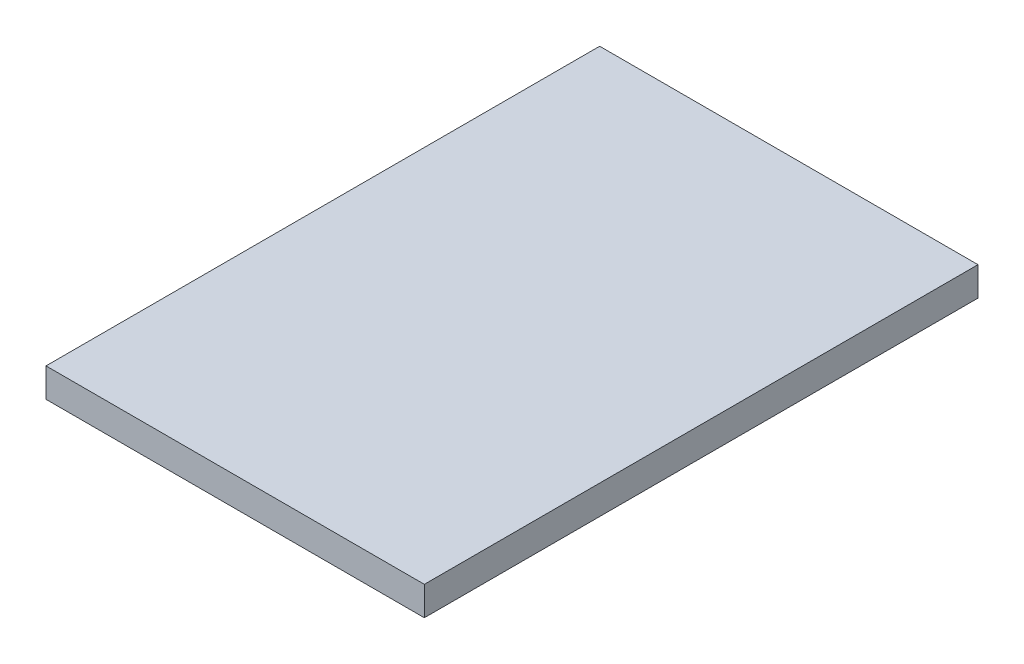
SolidWorks part; units mm, degrees
ref_plane "Front Plane" through (0, 0, 0) normal (0, 0, 1) x (1, 0, 0)
ref_plane "Top Plane" through (0, 0, 0) normal (0, 1, 0) x (1, 0, 0)
ref_plane "Right Plane" through (0, 0, 0) normal (1, 0, 0) x (0, 0, -1)
sketch "Sketch1" plane through (0, 0, 0) normal (0, 1, 0) x (1, 0, 0)
  line L1 (0, 0) -> (20.5, 0)
  line L2 (0, 0) -> (0, 30)
  line L3 (0, 30) -> (20.5, 30)
  line L4 (20.5, 0) -> (20.5, 30)
  dimension "D1" = 20.5
  dimension "D2" = 30
extrude "Boss-Extrude1" add sketch "Sketch1" along normal blind 1.57
sketch "Sketch2" plane through (0, 1.57, 0) normal (0, 1, 0) x (1, 0, 0)
  line L0 (0, 30) -> (0, 0) construction
  line L1 (0, 0) -> (20.5, 0) construction
  circle A0 centre (12.25, 3.5) radius 2.25
  dimension "D3" = 4.5
  dimension "D1" = 12.25
  dimension "D2" = 3.5
